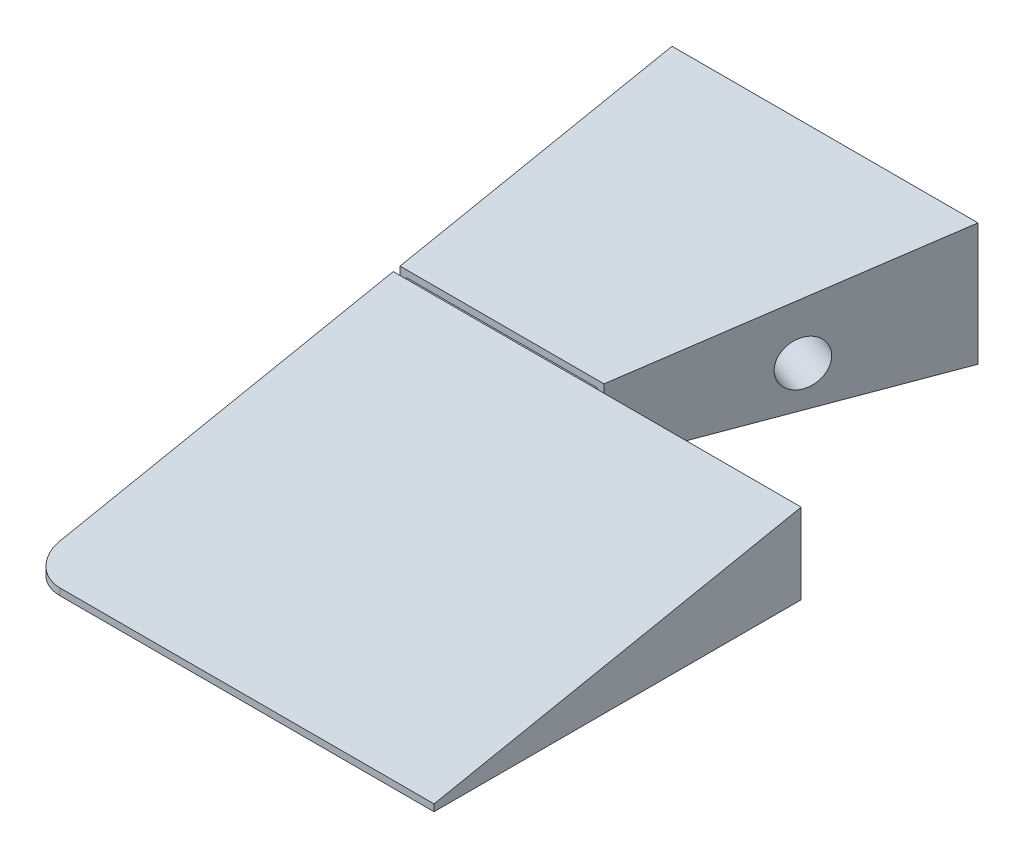
SolidWorks part; units mm, degrees
material "AISI 1020"
ref_plane "Plano frontal" through (0, 0, 0) normal (0, 0, 1) x (1, 0, 0)
ref_plane "Plano superior" through (0, 0, 0) normal (0, 1, 0) x (1, 0, 0)
ref_plane "Plano direito" through (0, 0, 0) normal (1, 0, 0) x (0, 0, -1)
sketch "Esboço1" plane through (0, 0, 0) normal (0, 0, 1) x (1, 0, 0)
  line L1 (-65, 10) -> (65, 10)
  line L2 (-65, 10) -> (-65, -10)
  line L3 (-65, -10) -> (65, -10)
  line L4 (65, 10) -> (65, -10)
  line L5 (-65, 10) -> (65, -10) construction
  line L6 (-65, -10) -> (65, 10) construction
  point P0 (0, 0)
  dimension "D1" = 130
  dimension "D2" = 20
extrude "Ressalto-extrusão1" add sketch "Esboço1" along normal blind 95
sketch "Esboço2" plane through (0, 10, 0) normal (0, 1, 0) x (1, 0, 0)
  line L0 (65, 0) -> (-20, 0)
  line L2 (-65, -95) -> (-65, 0) construction
  line L3 (-35, -40) -> (-20, 0)
  line L4 (65, 0) -> (-65, 0) construction
  line L9 (-35, -40) -> (-35, -41)
  line L10 (65, -95) -> (-65, -95) construction
  line L11 (-5, -95) -> (65, -95)
  line L12 (65, -95) -> (65, 0)
  line L13 (-35, -41) -> (-5, -41)
  line L14 (-5, -41) -> (-5, -95)
  dimension "D5" = 1
  dimension "D1" = 45
  dimension "D2" = 30
  dimension "D3" = 60
  dimension "D4" = 40
extrude "Corte-extrusão2" cut sketch "Esboço2" against normal up to next contours L3 L0 L12 L11 L14 L13 L9
sketch "Esboço13" plane through (-65, 0, 0) normal (-1, 0, 0) x (0, 0, 1)
  line L0 (0, 10) -> (95, -9)
  line L1 (95, 10) -> (95, -10) construction
  dimension "D1" = 1
extrude "Corte-extrusão4" cut sketch "Esboço13" against normal through all and the other way through all
hole_wizard "Broca de rosquear de cano para tarraxa de 1/84" positions "Esboço14" profile "Esboço15" hole size "1/8" standard "Ansi Inch"
sketch "Esboço14" plane through (-65, 0, 0) normal (-1, 0, 0) x (0, 0, 1)
  line L0 (0, 10) -> (0, -10) construction
  line L1 (95, -10) -> (0, -10) construction
  point P0 (20, -2)
  dimension "D1" = 20
  dimension "D2" = 8
sketch "Esboço15" plane through (-65, -2, 20) normal (0, 1, 0) x (0, 0, 1)
  line L0 (0, 0) -> (0, 11.9768)
  line L1 (0, 11.9768) -> (3.29, 10)
  line L2 (3.29, 10) -> (3.29, 0)
  line L5 (3.29, 0) -> (0, 0)
  line L10 (0, 11.9768) -> (-3.29, 10) construction
  line L11 (0, -6.35) -> (0, 107.95) construction
  dimension "Hole Dia." = 6.58
  dimension "Hole Depth" = 10
  dimension "Drill Angle" = 118
hole_wizard "Broca de rosquear de cano para tarraxa de 1/85" positions "Esboço16" profile "Esboço17" hole size "1/8" standard "Ansi Inch"
sketch "Esboço16" plane through (-17.5342, 0, -6.5753) normal (0.9363, 0, 0.3511) x (0.3511, 0, -0.9363)
  line L0 (-7.0225, -10) -> (-7.0225, 10) construction
  line L1 (-7.0225, -10) -> (-49.7425, -10) construction
  point P0 (-27.0225, -2)
  dimension "D1" = 20
  dimension "D2" = 8
sketch "Esboço17" plane through (-27.0225, -2, 18.7266) normal (0, 1, 0) x (0.3511, 0, -0.9363)
  line L0 (0, 0) -> (0, 11.9768)
  line L1 (0, 11.9768) -> (3.29, 10)
  line L2 (3.29, 10) -> (3.29, 0)
  line L5 (3.29, 0) -> (0, 0)
  line L10 (0, 11.9768) -> (-3.29, 10) construction
  line L11 (0, -6.35) -> (0, 107.95) construction
  dimension "Hole Dia." = 6.58
  dimension "Hole Depth" = 10
  dimension "Drill Angle" = 118
fillet "Filete2" radius 5 1 edges at (-65, -9.5, 95)
sketch "Esboço40" plane through (-65, 0, 0) normal (-1, 0, 0) x (0, 0, 1)
  line L0 (41, 1.8) -> (41, -10)
  line L1 (90, -10) -> (0, -10) construction
  line L2 (41, -10) -> (40, -10)
  line L3 (40, -10) -> (40, 2)
  line L4 (0, 10) -> (90, -8) construction
  line L5 (40, 2) -> (41, 1.8)
  line L6 (41, -10) -> (41, 1.8) construction
extrude "Corte-extrusão10" cut sketch "Esboço40" against normal up to next
sketch "Esboço41" plane through (0, 0, 40) normal (0, 0, 1) x (1, 0, 0)
  line L0 (-35, -10) -> (-35, 2) construction
  line L1 (-64, 1) -> (-36, 1)
  line L2 (-64, 1) -> (-64, -7)
  line L3 (-64, -7) -> (-36, -7)
  line L4 (-36, 1) -> (-36, -7)
  line L5 (-64, 1) -> (-36, -7) construction
  line L6 (-64, -7) -> (-36, 1) construction
  line L7 (-35, -10) -> (-65, -10) construction
  line L8 (-65, 2) -> (-65, -10) construction
  line L9 (-35, 2) -> (-65, 2) construction
  point P0 (-50, -3)
  point P13 (-50, 2)
  dimension "D1" = 1
  dimension "D2" = 3
  dimension "D3" = 1
  dimension "D4" = 1
extrude "Ressalto-extrusão2" add sketch "Esboço41" along normal up to next
sketch "Esboço42" plane through (0, 0, 0) normal (0, 0, -1) x (-1, 0, 0)
  line L0 (20, -10) -> (20, -8)
  line L1 (20, -8) -> (65, -8)
  line L2 (65, 10) -> (65, -10) construction
  line L3 (65, -8) -> (65, -10)
  line L4 (65, -10) -> (20, -10)
  dimension "D1" = 2
extrude "Corte-extrusão11" cut sketch "Esboço42" against normal blind 41
